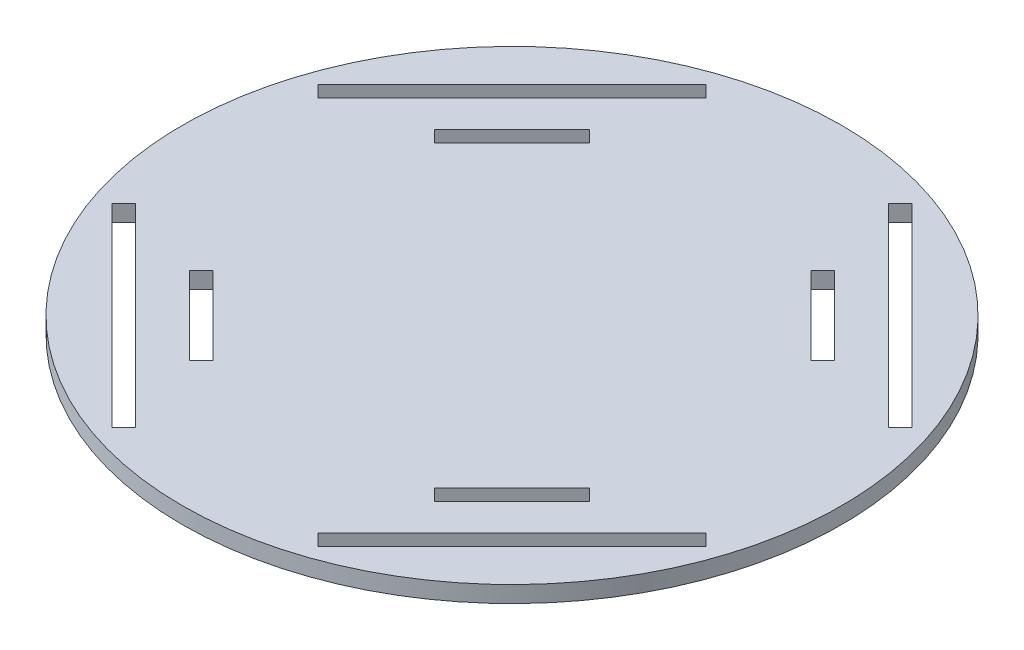
SolidWorks part; units mm, degrees
material "Acrylic (Medium-high impact)"
ref_plane "Plano frontal," through (0, 0, 0) normal (0, 0, 1) x (1, 0, 0)
ref_plane "Plano superior" through (0, 0, 0) normal (0, 1, 0) x (1, 0, 0)
ref_plane "Plano direito" through (0, 0, 0) normal (1, 0, 0) x (0, 0, -1)
sketch "Sketch1" plane through (0, 0, 0) normal (0, 1, 0) x (1, 0, 0)
  circle A0 centre (0, 0) radius 60
  dimension "D1" = 120
extrude "Boss-Extrude1" add sketch "Sketch1" along normal mid plane 3
sketch "Sketch4" plane through (0, 1.5, 0) normal (0, 1, 0) x (1, 0, 0)
  line L0 (16.617, 51.9723) -> (51.9723, 16.617)
  line L1 (16.617, 51.9723) -> (18.7383, 54.0937)
  line L2 (51.9723, 16.617) -> (54.0937, 18.7383)
  line L3 (18.7383, 54.0937) -> (54.0937, 18.7383)
  line L4 (16.617, 51.9723) -> (54.0937, 18.7383) construction
  line L5 (51.9723, 16.617) -> (18.7383, 54.0937) construction
  line L6 (0, 0) -> (35.3553, 35.3553) construction
  point P1 (35.3553, 35.3553)
  dimension "D1" = 3
  dimension "D2" = 50
  dimension "D3" = 50
  dimension "D4" = 45
extrude "Cut-Extrude3" cut sketch "Sketch4" against normal through all both and the other way through all
pattern_circular "CirPattern1" count 4 over 360 about axis through (0, 0, 0) along (0, 1, 0) of "Cut-Extrude3"
sketch "Sketch5" plane through (0, 1.5, 0) normal (0, 1, 0) x (1, 0, 0)
  line L0 (22.2739, 36.416) -> (36.416, 22.2739)
  line L1 (22.2739, 36.416) -> (20.1525, 34.2947)
  line L2 (36.416, 22.2739) -> (34.2947, 20.1525)
  line L3 (20.1525, 34.2947) -> (34.2947, 20.1525)
  line L4 (22.2739, 36.416) -> (34.2947, 20.1525) construction
  line L5 (36.416, 22.2739) -> (20.1525, 34.2947) construction
  line L7 (54.0937, 18.7383) -> (18.7383, 54.0937) construction
  line L8 (0, 0) -> (28.2843, 28.2843) construction
  point P1 (28.2843, 28.2843)
  dimension "D1" = 3
  dimension "D2" = 20
  dimension "D3" = 40
extrude "Cut-Extrude4" cut sketch "Sketch5" against normal through all
pattern_circular "CirPattern2" count 4 over 360 about axis through (0, 0, 0) along (0, 1, 0) of "Cut-Extrude4"
